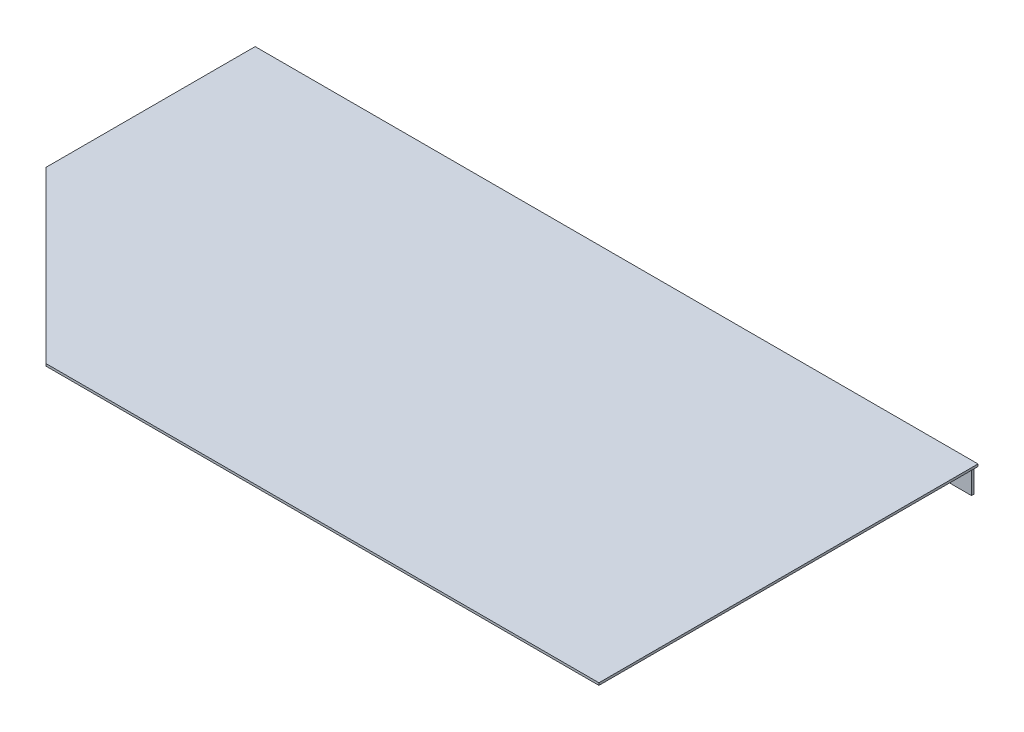
SolidWorks part; units mm, degrees
material "PPS"
ref_plane "Płaszczyzna XY" through (0, 0, 0) normal (0, 0, 1) x (1, 0, 0)
ref_plane "Płaszczyzna XZ" through (0, 0, 0) normal (0, 1, 0) x (1, 0, 0)
ref_plane "Płaszczyzna YZ" through (0, 0, 0) normal (1, 0, 0) x (0, 0, -1)
sketch "Szkic2" plane through (0, 0, 0) normal (0, 0, 1) x (1, 0, 0)
  line L0 (-276.5, 0) -> (276.5, 0)
  line L1 (-276.5, 0) -> (-276.5, -1.75)
  line L2 (276.5, 0) -> (276.5, -1.75)
  line L3 (276.5, -1.75) -> (-276.5, -1.75)
  point P4 (0, 0)
  dimension "D1" = 553
  dimension "D2" = 1.75
  dimension "D3" = 90
  dimension "D4" = 90
extrude "Dodanie-wyciągnięcie1" add sketch "Szkic2" along normal blind 290
sketch "Szkic3" plane through (0, 0, 0) normal (0, 1, 0) x (1, 0, 0)
  line L0 (-276.5, -290) -> (-276.5, -160)
  line L1 (276.5, -290) -> (-276.5, -290) construction
  line L2 (-276.5, -290) -> (-276.5, 0) construction
  line L3 (-276.5, -160) -> (-146.5, -290)
  line L4 (-146.5, -290) -> (-276.5, -290)
  dimension "D1" = 130
  dimension "D2" = 130
  dimension "D3" = 90
extrude "Wytnij-wyciągnięcie1" cut sketch "Szkic3" against normal blind 10
sketch "Szkic7" plane through (0, -1.75, 0) normal (0, -1, 0) x (1, 0, 0)
  line L0 (-274.75, 1.75) -> (-274.75, 0)
  line L1 (-274.75, 0) -> (273.25, 0)
  line L2 (273.25, 0) -> (273.25, 1.75)
  line L3 (273.25, 1.75) -> (-274.75, 1.75)
  line L4 (-276.5, 0) -> (276.5, 0) construction
  line L5 (-276.5, 160) -> (-276.5, 0) construction
  dimension "D1" = 548
  dimension "D2" = 1.75
  dimension "D3" = 0
  dimension "D4" = 1.75
extrude "Dodanie-wyciągnięcie4" add sketch "Szkic7" along normal blind 20
